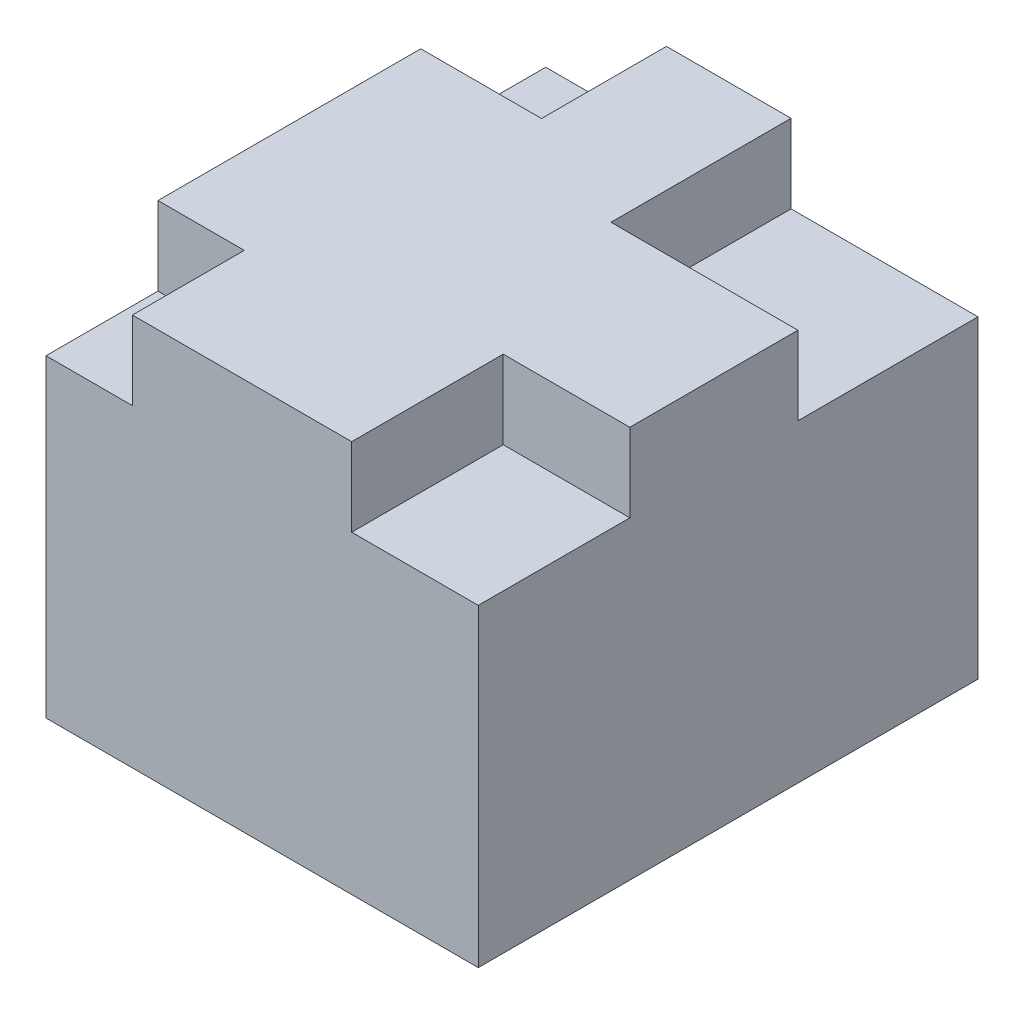
SolidWorks part; units mm, degrees
ref_plane "Front Plane" through (0, 0, 0) normal (0, 0, 1) x (1, 0, 0)
ref_plane "Top Plane" through (0, 0, 0) normal (0, 1, 0) x (1, 0, 0)
ref_plane "Right Plane" through (0, 0, 0) normal (1, 0, 0) x (0, 0, -1)
sketch "Sketch1" plane through (0, 0, 0) normal (0, 1, 0) x (1, 0, 0)
  line L1 (5.5106, -6.3702) -> (-5.5106, -6.3702)
  line L2 (5.5106, -6.3702) -> (5.5106, 6.3702)
  line L3 (5.5106, 6.3702) -> (-5.5106, 6.3702)
  line L4 (-5.5106, -6.3702) -> (-5.5106, 6.3702)
  line L5 (5.5106, -6.3702) -> (-5.5106, 6.3702) construction
  line L6 (5.5106, 6.3702) -> (-5.5106, -6.3702) construction
  point P0 (0, 0)
extrude "Boss-Extrude1" add sketch "Sketch1" along normal blind 10
sketch "Sketch2" plane through (0, 10, 0) normal (0, 1, 0) x (1, 0, 0)
  line L1 (-5.5106, -6.3702) -> (-3.309, -6.3702)
  line L2 (-5.5106, -6.3702) -> (-5.5106, -3.5158)
  line L3 (-5.5106, -3.5158) -> (-3.309, -3.5158)
  line L4 (-3.309, -6.3702) -> (-3.309, -3.5158)
  line L5 (5.5106, -6.3702) -> (2.2832, -6.3702)
  line L6 (5.5106, -6.3702) -> (5.5106, -2.5066)
  line L7 (5.5106, -2.5066) -> (2.2832, -2.5066)
  line L8 (2.2832, -6.3702) -> (2.2832, -2.5066)
  line L9 (-5.5106, 6.3702) -> (-2.4321, 6.3702)
  line L10 (-5.5106, 6.3702) -> (-5.5106, 3.1849)
  line L11 (-5.5106, 3.1849) -> (-2.4321, 3.1849)
  line L12 (-2.4321, 6.3702) -> (-2.4321, 3.1849)
  line L13 (5.5106, 6.3702) -> (0.7445, 6.3702)
  line L14 (5.5106, 6.3702) -> (5.5106, 1.7786)
  line L15 (5.5106, 1.7786) -> (0.7445, 1.7786)
  line L16 (0.7445, 6.3702) -> (0.7445, 1.7786)
extrude "Cut-Extrude1" cut sketch "Sketch2" against normal blind 2
sketch "Sketch3" plane through (0, 0, 0) normal (0, -1, 0) x (1, 0, 0)
  line L1 (2.1012, -2.1757) -> (-2.1012, -2.1757)
  line L2 (2.1012, -2.1757) -> (2.1012, 2.1757)
  line L3 (2.1012, 2.1757) -> (-2.1012, 2.1757)
  line L4 (-2.1012, -2.1757) -> (-2.1012, 2.1757)
  line L5 (2.1012, -2.1757) -> (-2.1012, 2.1757) construction
  line L6 (2.1012, 2.1757) -> (-2.1012, -2.1757) construction
  point P0 (0, 0)
extrude "Cut-Extrude2" cut sketch "Sketch3" against normal blind 5
